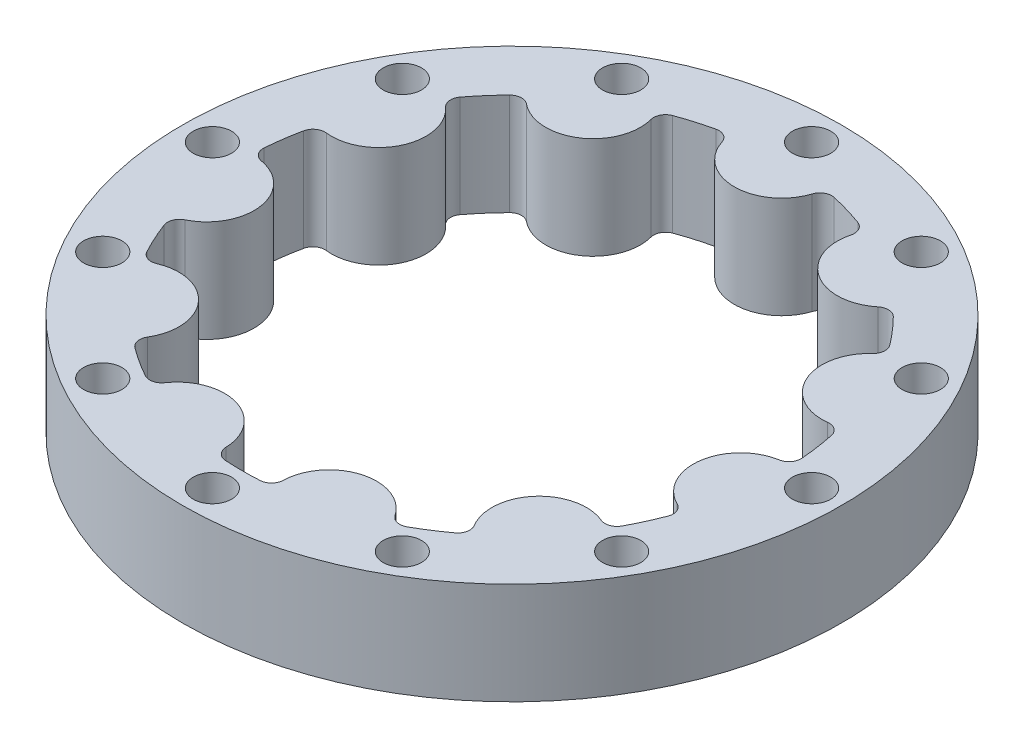
SolidWorks part; units mm, degrees
ref_plane "Front Plane" through (0, 0, 0) normal (0, 0, 1) x (1, 0, 0)
ref_plane "Top Plane" through (0, 0, 0) normal (0, 1, 0) x (1, 0, 0)
ref_plane "Right Plane" through (0, 0, 0) normal (1, 0, 0) x (0, 0, -1)
sketch "Sketch1" plane through (0, 0, 0) normal (0, 1, 0) x (1, 0, 0)
  line L0 (0, 22.5) -> (0, 0) construction
  line L1 (0, 0) -> (12.1644, 18.9282) construction
  line L2 (0, 0) -> (-12.1644, 18.9282) construction
  line L3 (-20.4667, 9.3468) -> (0, 0) construction
  line L4 (0, 0) -> (-22.271, -3.2021) construction
  circle A0 centre (0, 0) radius 22.5
  circle A1 centre (0, 0) radius 27.5
  circle A2 centre (0, 22.5) radius 3.95
  circle A3 centre (12.1644, 18.9282) radius 3.95
  circle A4 centre (20.4667, 9.3468) radius 3.95
  circle A5 centre (22.271, -3.2021) radius 3.95
  circle A6 centre (17.0044, -14.7344) radius 3.95
  circle A7 centre (6.339, -21.5886) radius 3.95
  circle A8 centre (-6.339, -21.5886) radius 3.95
  circle A9 centre (-17.0044, -14.7344) radius 3.95
  circle A10 centre (-22.271, -3.2021) radius 3.95
  circle A11 centre (-20.4667, 9.3468) radius 3.95
  circle A12 centre (-12.1644, 18.9282) radius 3.95
  point P27 (0, 0)
  dimension "D1" = 45
  dimension "D2" = 55
  dimension "D3" = 7.9
  dimension "D4" = 11
extrude "Boss-Extrude2" add sketch "Sketch1" along normal blind 8.5 contours A1 A12 A0 A2 A3 A4 A5 A6 A7 A8 A9 A10 A11 | A0 A11 | A0 A11 | A0 A12 | A0 A12 | A0 A2 | A0 A2 | A0 A3 | A0 A3 | A0 A4 | A0 A4 | A0 A5 | A0 A5 | A0 A6 | A0 A6 | A0 A7 | A0 A7 | A0 A8 | A0 A8 | A0 A9 | A0 A9 | A0 A10 | A0 A10
fillet "Fillet2" radius 1 22 edges at (14.1656, 4.25, 17.481) (19.319, 4.25, 11.5336) (2.4659, 4.25, 22.3645) (10.0167, 4.25, 20.1474) (-10.0167, 4.25, 20.1474) (-2.4659, 4.25, 22.3645) (-19.319, 4.25, 11.5336) (-14.1656, 4.25, 17.481) (-22.4878, 4.25, -0.742) (-21.3678, 4.25, 7.0474) (-18.5168, 4.25, -12.782) (-21.7859, 4.25, -5.6236) (-8.6668, 4.25, -20.7638) (-15.2871, 4.25, -16.5092) (3.9348, 4.25, -22.1533) (-3.9348, 4.25, -22.1533) (15.2871, 4.25, -16.5092) (8.6668, 4.25, -20.7638) (21.7859, 4.25, -5.6236) (18.5168, 4.25, -12.782) (21.3678, 4.25, 7.0474) (22.4878, 4.25, -0.742)
sketch "Sketch2" plane through (0, 0, 0) normal (0, -1, 0) x (1, 0, 0)
  circle A0 centre (0, 0) radius 25 construction
  circle A1 centre (25, 0) radius 1.6
  circle A2 centre (21.6506, -12.5) radius 1.6
  circle A3 centre (12.5, -21.6506) radius 1.6
  circle A4 centre (0, -25) radius 1.6
  circle A5 centre (-12.5, -21.6506) radius 1.6
  circle A6 centre (-21.6506, -12.5) radius 1.6
  circle A7 centre (-25, 0) radius 1.6
  circle A8 centre (-21.6506, 12.5) radius 1.6
  circle A9 centre (-12.5, 21.6506) radius 1.6
  circle A10 centre (0, 25) radius 1.6
  circle A11 centre (12.5, 21.6506) radius 1.6
  circle A12 centre (21.6506, 12.5) radius 1.6
  point P29 (0, 0)
  dimension "D1" = 50
  dimension "D2" = 3.2
  dimension "D3" = 12
extrude "Cut-Extrude1" cut sketch "Sketch2" against normal blind 10
